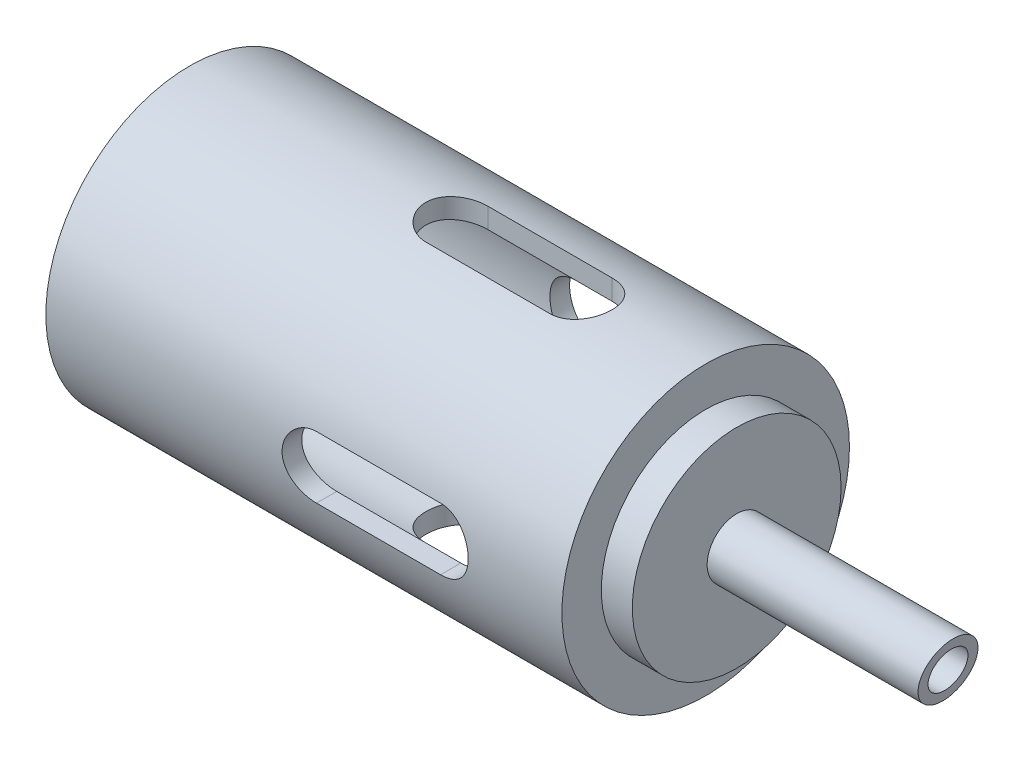
SolidWorks part; units mm, degrees
ref_plane "Alzado" through (0, 0, 0) normal (0, 0, 1) x (1, 0, 0)
ref_plane "Planta" through (0, 0, 0) normal (0, 1, 0) x (1, 0, 0)
ref_plane "Vista lateral" through (0, 0, 0) normal (1, 0, 0) x (0, 0, -1)
sketch "Croquis1" plane through (0, 0, 0) normal (0, 0, 1) x (1, 0, 0)
  line L0 (0, 0) -> (-65.0368, 0) construction
  line L1 (-61.5381, 11.5875) -> (-19.9481, 11.5875)
  line L2 (-19.9481, 11.5875) -> (-19.9481, 8.4125)
  line L3 (-61.5381, 11.5875) -> (-61.5381, 10)
  line L4 (-61.5381, 10) -> (-21.5381, 10)
  line L5 (-19.9481, 8.4125) -> (-17.4481, 8.4125)
  line L6 (-17.4481, 8.4125) -> (-17.4481, 2.3812)
  line L7 (-17.4481, 1.5875) -> (-21.5381, 1.5875)
  line L8 (-21.5381, 1.5875) -> (-21.5381, 10)
  line L9 (-17.4481, 1.5875) -> (0, 1.5875)
  line L10 (0, 1.5875) -> (0, 2.3812)
  line L11 (0, 2.3812) -> (-17.4481, 2.3812)
  point P14 (-19.9481, 10)
  dimension "D1" = 1.5875
  dimension "D2" = 10
  dimension "D3" = 1.5875
  dimension "D4" = 0.7937
  dimension "D5" = 40
  dimension "D6" = 1.59
  dimension "D7" = 2.5
revolve "Revolución1" add sketch "Croquis1" angle 360 about L0
sketch "Croquis2" plane through (0, 0, 0) normal (0, 0, 1) x (1, 0, 0)
  line L1 (-40, 2.5) -> (-30, 2.5)
  line L3 (-40, -2.5) -> (-30, -2.5)
  arc A0 (-40, 2.5) -> (-40, -2.5) centre (-40, 0) ccw
  arc A1 (-30, 2.5) -> (-30, -2.5) centre (-30, 0) cw
  dimension "D1" = 10
  dimension "D2" = 5
  dimension "D3" = 30
extrude "Cortar-Extruir1" cut sketch "Croquis2" against normal through all both and the other way through all
sketch "Croquis3" plane through (0, 0, 0) normal (0, 1, 0) x (1, 0, 0)
  line L1 (-40, 2.5) -> (-30, 2.5)
  line L3 (-40, -2.5) -> (-30, -2.5)
  arc A0 (-40, 2.5) -> (-40, -2.5) centre (-40, 0) ccw
  arc A1 (-30, 2.5) -> (-30, -2.5) centre (-30, 0) cw
  dimension "D1" = 5
  dimension "D2" = 10
  dimension "D3" = 30
extrude "Cortar-Extruir2" cut sketch "Croquis3" against normal through all both and the other way through all
sketch "Croquis4" plane through (0, 0, 0) normal (0, 0, 1) x (1, 0, 0)
  line L0 (0, 2.3812) -> (-0.8398, -2.3812)
  line L1 (-17.4481, -2.3812) -> (0, -2.3812) construction
  line L2 (-0.8398, -2.3812) -> (0, -2.3812)
  line L3 (0, -2.3812) -> (0, 2.3812)
  dimension "D1" = 10
extrude "Cortar-Extruir3" cut sketch "Croquis4" against normal through all both and the other way through all
